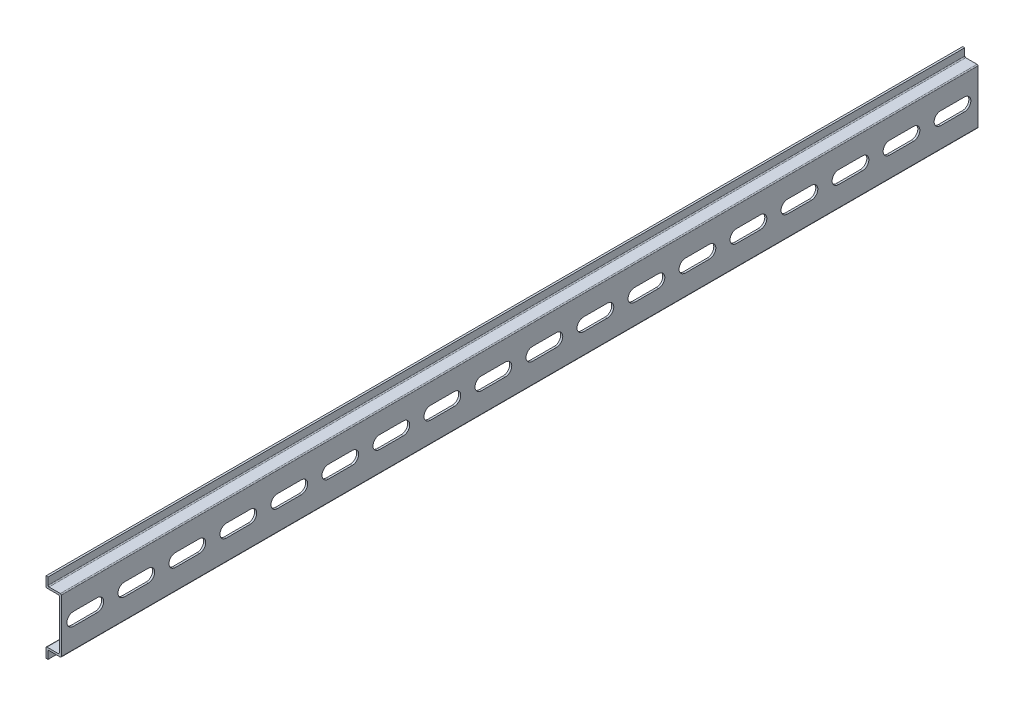
SolidWorks part; units mm, degrees
ref_plane "Front Plane" through (0, 0, 0) normal (0, 0, 1) x (1, 0, 0)
ref_plane "Top Plane" through (0, 0, 0) normal (0, 1, 0) x (1, 0, 0)
ref_plane "Right Plane" through (0, 0, 0) normal (1, 0, 0) x (0, 0, -1)
sketch "profile" plane through (0, 0, 0) normal (0, 0, 1) x (1, 0, 0)
  line L0 (0, -13.5) -> (0, 13.5) construction
  line L1 (0, 13.5) -> (-6.5, 13.5) construction
  line L2 (-6.5, 13.5) -> (-6.5, 17.5) construction
  line L3 (0, -13.5) -> (-6.5, -13.5) construction
  line L4 (-6.5, -13.5) -> (-6.5, -17.5) construction
  dimension "D1" = 27
  dimension "D2" = 35
  dimension "D3" = 6.5
sketch "Sketch3" plane through (0, 0, 0) normal (0, 0, 1) x (1, 0, 0)
  line L0 (-6.5, -13.5) -> (-6.5, -17.5) construction
  line L1 (0, -13.5) -> (-6.5, -13.5) construction
  line L2 (0, -13.5) -> (0, 13.5) construction
  line L3 (0, 13.5) -> (-6.5, 13.5) construction
  line L4 (-6.5, 13.5) -> (-6.5, 17.5) construction
  line L5 (-6.5, -13.5) -> (-6.5, -17.5)
  line L6 (0, -13.5) -> (-6.5, -13.5)
  line L7 (0, -13.5) -> (0, 13.5)
  line L8 (0, 13.5) -> (-6.5, 13.5)
  line L9 (-6.5, 13.5) -> (-6.5, 17.5)
extrude "Extrude-Thin1" add sketch "Sketch3" along normal blind 449.2625 thin
sketch "Sketch4" plane through (0, 0, 0) normal (1, 0, 0) x (0, 0, -1)
  line L0 (0, 0) -> (-62.1077, 0) construction
  line L1 (-6.65, 0) -> (-18.35, 0) construction
  line L2 (-6.65, -3.15) -> (-18.35, -3.15)
  line L3 (-6.65, 3.15) -> (-18.35, 3.15)
  arc A0 (-6.65, -3.15) -> (-6.65, 3.15) centre (-6.65, 0) ccw
  arc A1 (-18.35, 3.15) -> (-18.35, -3.15) centre (-18.35, 0) ccw
  point P5 (-12.5, 0)
  point P10 (-3.5, 0)
  point P11 (-21.5, 0)
  point P12 (-37.5, 0)
  dimension "D1" = 18
  dimension "D2" = 6.3
  dimension "D3" = 12.5
  dimension "D4" = 25
extrude "Cut-Extrude1" cut sketch "Sketch4" against normal through all both and the other way through all
pattern_linear "LPattern1" count 18 spacing 25 along (0, 0, 1) of "Cut-Extrude1"
fillet "Fillet1" radius 0.5 8 edges at (0, -13.5, 224.6312) (0, 13.5, 224.6312) (-6.5, 13.5, 224.6312) (-6.5, -13.5, 224.6312) (-1, 12.5, 224.6312) (-1, -12.5, 224.6312) (-7.5, -12.5, 224.6312) (-7.5, 12.5, 224.6312)
ref_plane "Contact Plane 1" through (-1, 0, 0) normal (-1, 0, 0) x (0, 0, 1)
equation "\"D3@LPattern1\"=\"D4@Sketch4\""
equation "\"D1@LPattern1\" = \"Length@Extrude-Thin1\" / \"D3@LPattern1\""
